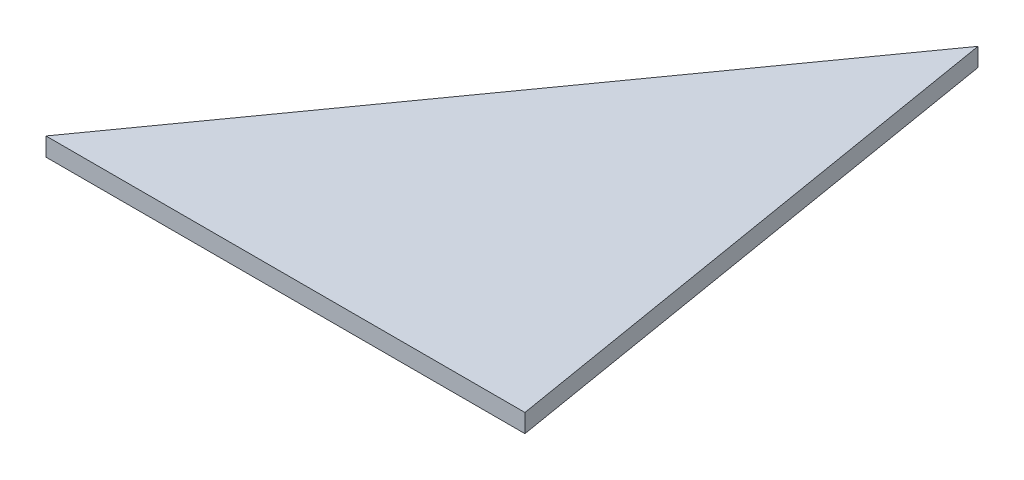
SolidWorks part; units mm, degrees
ref_plane "Plan de face" through (0, 0, 0) normal (0, 0, 1) x (1, 0, 0)
ref_plane "Plan de dessus" through (0, 0, 0) normal (0, 1, 0) x (1, 0, 0)
ref_plane "Plan de droite" through (0, 0, 0) normal (1, 0, 0) x (0, 0, -1)
sketch "Esquisse1" plane through (0, 0, 0) normal (0, 1, 0) x (1, 0, 0)
  line L0 (0, 0) -> (52.1405, 0)
  line L1 (52.1405, 0) -> (42.2806, 59.1843)
  line L2 (42.2806, 59.1843) -> (0, 0)
  point P3 (0, 0)
extrude "Boss.-Extru.1" add sketch "Esquisse1" along normal blind 2
